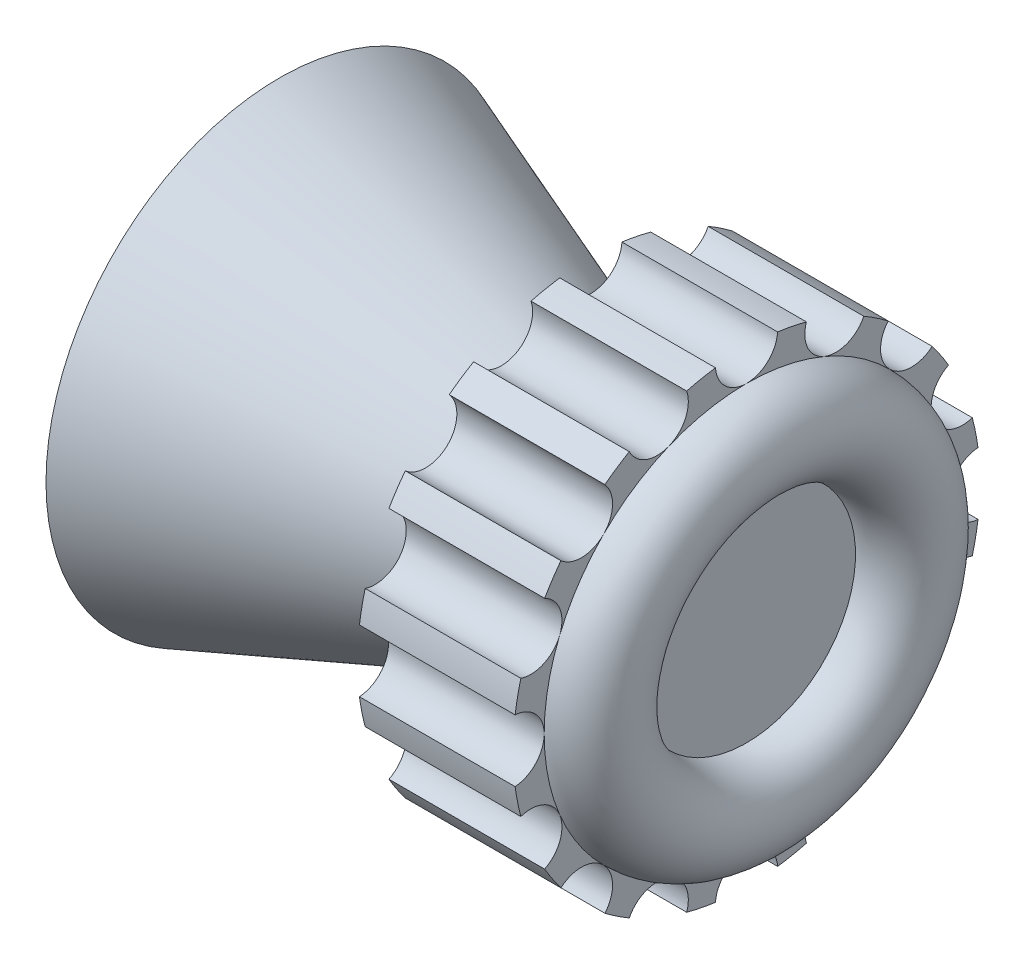
SolidWorks part; units mm, degrees
ref_plane "Front Plane" through (0, 0, 0) normal (0, 0, 1) x (1, 0, 0)
ref_plane "Top Plane" through (0, 0, 0) normal (0, 1, 0) x (1, 0, 0)
ref_plane "Right Plane" through (0, 0, 0) normal (1, 0, 0) x (0, 0, -1)
sketch "Sketch1" plane through (0, 0, 0) normal (0, 0, 1) x (1, 0, 0)
  line L0 (-16.375, 0) -> (24.375, 0) construction
  line L1 (-4.75, 5.5) -> (-4.75, 7.5)
  line L2 (-4.75, 7.5) -> (5.25, 3.7559)
  line L3 (10.25, 2.5) -> (10.25, 0)
  line L6 (7.25, 2) -> (7.25, 0)
  line L7 (7.25, 0) -> (10.25, 0)
  line L8 (0.25, 2) -> (7.25, 2)
  line L9 (0.25, 3.75) -> (0.25, 2)
  line L17 (-4.75, 5.5) -> (0.25, 3.75)
  line L18 (5.25, 3.7559) -> (5.25, 7.5)
  line L19 (5.25, 7.5) -> (10.25, 7.5)
  line L20 (10.25, 7.5) -> (10.25, 6.5)
  line L21 (10.25, 3.5) -> (10.25, 2.5)
  arc A0 (10.25, 3.5) -> (10.25, 6.5) centre (10.25, 5) ccw
  point P3 (-4.75, 2)
  point P8 (2.5006, 2)
  point P12 (-14.75, 21.3743)
  point P14 (20.25, 9.7076)
  point P15 (20.25, -10)
  point P19 (-14.75, -8)
  dimension "D9" = 3
  dimension "D1" = 7
  dimension "D2" = 15
  dimension "D3" = 5
  dimension "D4" = 15
  dimension "D5" = 4
  dimension "D7" = 2
  dimension "D6" = 5
  dimension "D8" = 15
revolve "Revolve1" add sketch "Sketch1" angle 360 about L0
sketch "Sketch2" plane through (0.25, 0, 0) normal (-1, 0, 0) x (0, 0, 1)
  line L1 (1.1, 1.6703) -> (1.1, -1.6703)
  circle A5 centre (0, 0) radius 2 construction
  arc A6 (1.1, -1.6703) -> (1.1, 1.6703) centre (0, 0) ccw
extrude "Boss-Extrude1" add sketch "Sketch2" against normal up to surface (7 mm away) up to face at (7.25, 0, 2)
sketch "Sketch3" plane through (10.25, 0, 0) normal (1, 0, 0) x (0, 0, -1)
  arc A0 (-7.4333, -0.9978) -> (-7.4333, 0.9978) centre (-7.5, 0) ccw
  circle A1 centre (0, 0) radius 7.5 construction
  arc A2 (-7.2493, 1.9228) -> (-6.4857, 3.7664) centre (-6.9291, 2.8701) ccw
  arc A3 (-5.9617, 4.5506) -> (-4.5506, 5.9617) centre (-5.3033, 5.3033) ccw
  arc A4 (-3.7664, 6.4857) -> (-1.9228, 7.2493) centre (-2.8701, 6.9291) ccw
  arc A5 (-0.9978, 7.4333) -> (0.9978, 7.4333) centre (0, 7.5) ccw
  arc A6 (1.9228, 7.2493) -> (3.7664, 6.4857) centre (2.8701, 6.9291) ccw
  arc A7 (4.5506, 5.9617) -> (5.9617, 4.5506) centre (5.3033, 5.3033) ccw
  arc A8 (6.4857, 3.7664) -> (7.2493, 1.9228) centre (6.9291, 2.8701) ccw
  arc A9 (7.4333, 0.9978) -> (7.4333, -0.9978) centre (7.5, 0) ccw
  arc A10 (7.2493, -1.9228) -> (6.4857, -3.7664) centre (6.9291, -2.8701) ccw
  arc A11 (5.9617, -4.5506) -> (4.5506, -5.9617) centre (5.3033, -5.3033) ccw
  arc A12 (3.7664, -6.4857) -> (1.9228, -7.2493) centre (2.8701, -6.9291) ccw
  arc A13 (0.9978, -7.4333) -> (-0.9978, -7.4333) centre (0, -7.5) ccw
  arc A14 (-1.9228, -7.2493) -> (-3.7664, -6.4857) centre (-2.8701, -6.9291) ccw
  arc A15 (-4.5506, -5.9617) -> (-5.9617, -4.5506) centre (-5.3033, -5.3033) ccw
  arc A16 (-6.4857, -3.7664) -> (-7.2493, -1.9228) centre (-6.9291, -2.8701) ccw
  circle A17 centre (0, 0) radius 7.5
  point P37 (0, 0)
  dimension "D1" = 2
  dimension "D2" = 16
extrude "Cut-Extrude1" cut sketch "Sketch3" along direction (1, 0, 0) on the side against the normal blind 5
